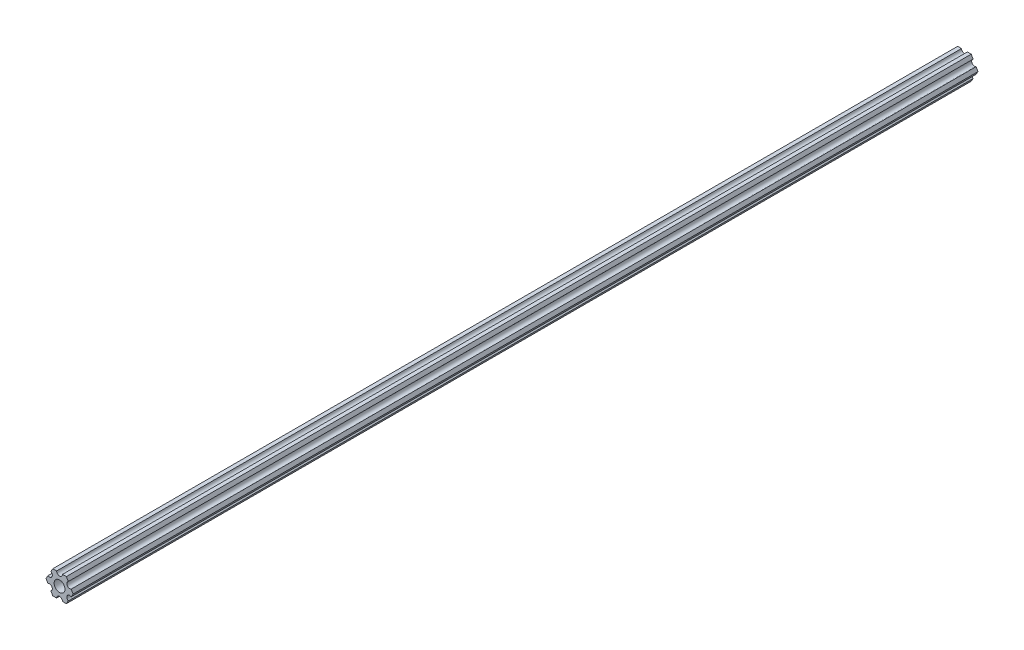
SolidWorks part; units mm, degrees
ref_plane "Front Plane" through (0, 0, 0) normal (0, 0, 1) x (1, 0, 0)
ref_plane "Top Plane" through (0, 0, 0) normal (0, 1, 0) x (1, 0, 0)
ref_plane "Right Plane" through (0, 0, 0) normal (1, 0, 0) x (0, 0, -1)
sketch "Sketch1" plane through (0, 0, 0) normal (0, 0, 1) x (1, 0, 0)
  line L0 (-1.5875, 6.35) -> (-3.6662, 6.35)
  line L1 (7.3323, 0) -> (6.293, 1.8002)
  line L2 (3.6662, 6.35) -> (1.5875, 6.35)
  line L3 (-3.6662, 6.35) -> (-4.7055, 4.5498)
  line L4 (-7.3323, 0) -> (-6.293, -1.8002)
  line L5 (-3.6662, -6.35) -> (-1.5875, -6.35)
  line L6 (3.6662, -6.35) -> (4.7055, -4.5498)
  line L7 (-6.293, 1.8002) -> (-7.3323, 0)
  line L8 (-4.7055, -4.5498) -> (-3.6662, -6.35)
  line L9 (1.5875, -6.35) -> (3.6662, -6.35)
  line L10 (6.293, -1.8002) -> (7.3323, 0)
  line L11 (4.7055, 4.5498) -> (3.6662, 6.35)
  circle A0 centre (0, 0) radius 2.9337
  arc A2 (-1.5875, 6.35) -> (1.5875, 6.35) centre (0, 6.35) ccw
  arc A3 (4.7055, 4.5498) -> (6.293, 1.8002) centre (5.4993, 3.175) ccw
  arc A4 (6.293, -1.8002) -> (4.7055, -4.5498) centre (5.4993, -3.175) ccw
  arc A5 (1.5875, -6.35) -> (-1.5875, -6.35) centre (0, -6.35) ccw
  arc A6 (-4.7055, -4.5498) -> (-6.293, -1.8002) centre (-5.4993, -3.175) ccw
  arc A7 (-6.293, 1.8002) -> (-4.7055, 4.5498) centre (-5.4993, 3.175) ccw
  dimension "D1" = 5.8674
  dimension "D3" = 3.175
  dimension "D4" = 6
extrude "Boss-Extrude1" add sketch "Sketch1" along normal blind 488.95
